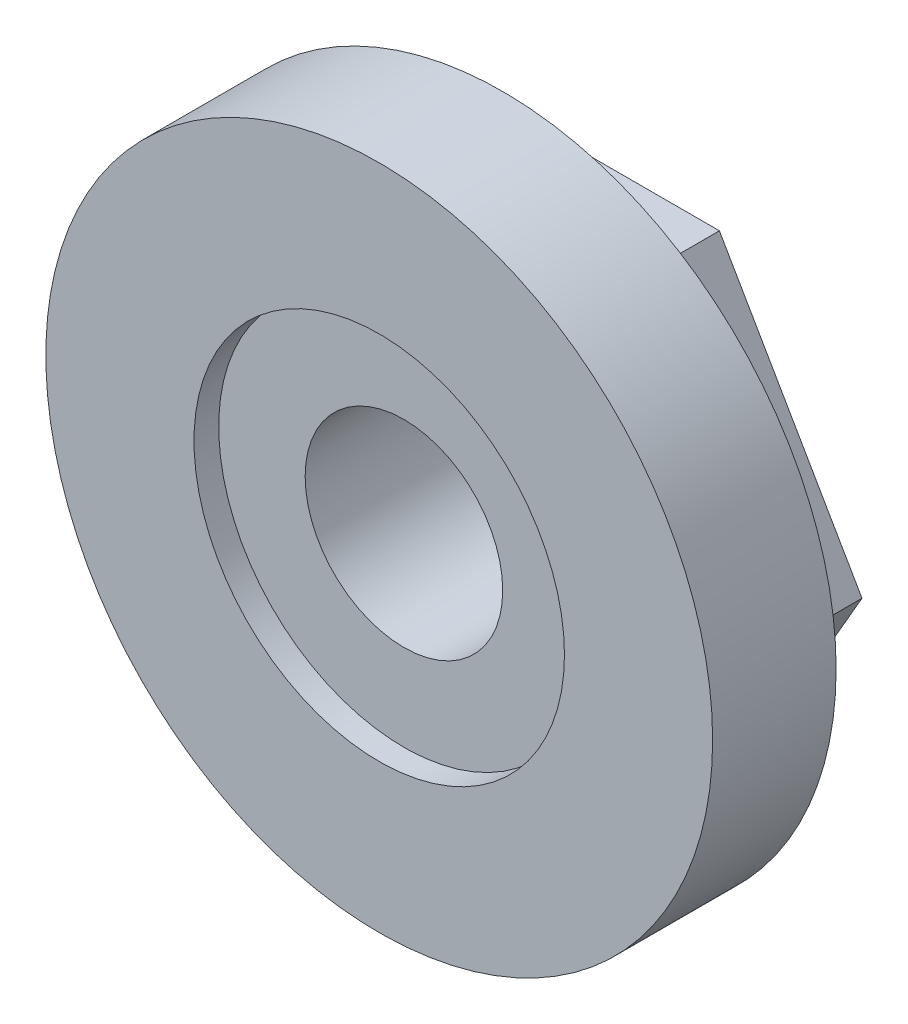
SolidWorks part; units mm, degrees
material "ABS"
ref_plane "Front Plane" through (0, 0, 0) normal (0, 0, 1) x (1, 0, 0)
ref_plane "Top Plane" through (0, 0, 0) normal (0, 1, 0) x (1, 0, 0)
ref_plane "Right Plane" through (0, 0, 0) normal (1, 0, 0) x (0, 0, -1)
sketch "Sketch1" plane through (0, 0, 0) normal (0, 0, 1) x (1, 0, 0)
  line L1 (5.7735, -10) -> (11.547, 0)
  line L2 (11.547, 0) -> (5.7735, 10)
  line L3 (5.7735, 10) -> (-5.7735, 10)
  line L4 (-5.7735, 10) -> (-11.547, 0)
  line L5 (-11.547, 0) -> (-5.7735, -10)
  line L6 (-5.7735, -10) -> (5.7735, -10)
  circle A0 centre (0, 0) radius 10 construction
  dimension "D1" = 20
extrude "Boss-Extrude1" add sketch "Sketch1" along normal blind 3
sketch "Sketch2" plane through (0, 0, 3) normal (0, 0, 1) x (1, 0, 0)
  circle A0 centre (0, 0) radius 13.5
  dimension "D1" = 27
extrude "Boss-Extrude2" add sketch "Sketch2" along normal blind 5
sketch "Sketch3" plane through (0, 0, 8) normal (0, 0, 1) x (1, 0, 0)
  circle A0 centre (0, 0) radius 7.5
  dimension "D1" = 15
extrude "Cut-Extrude1" cut sketch "Sketch3" against normal blind 1
sketch "Sketch4" plane through (0, 0, 0) normal (0, 0, -1) x (-1, 0, 0)
  circle A0 centre (0, 0) radius 4
  dimension "D1" = 8
extrude "Cut-Extrude2" cut sketch "Sketch4" against normal through all
